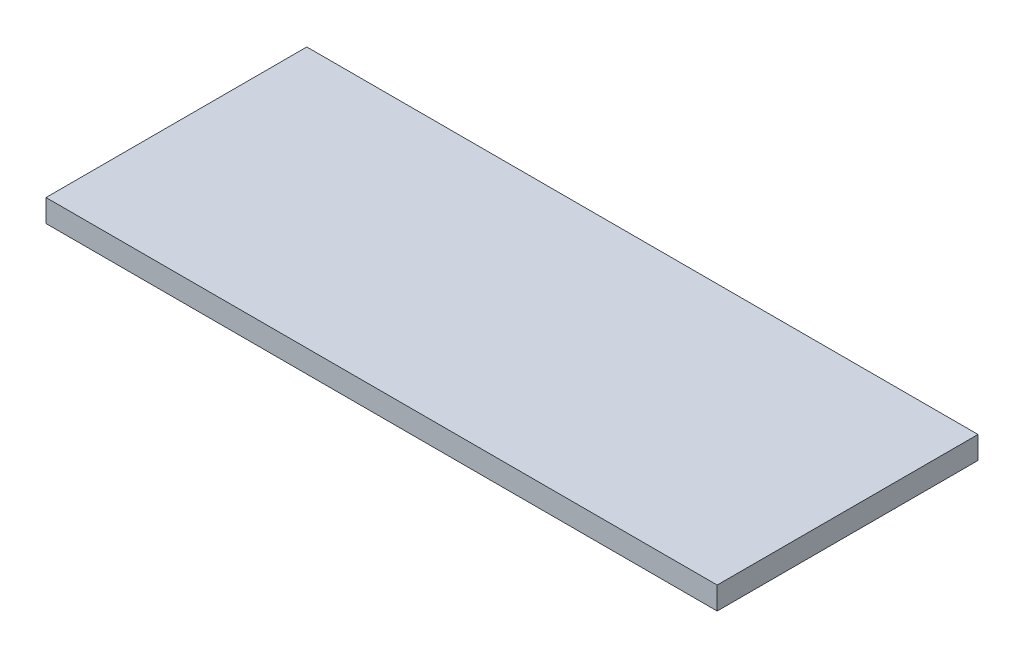
SolidWorks part; units mm, degrees
ref_plane "Front Plane" through (0, 0, 0) normal (0, 0, 1) x (1, 0, 0)
ref_plane "Top Plane" through (0, 0, 0) normal (0, 1, 0) x (1, 0, 0)
ref_plane "Right Plane" through (0, 0, 0) normal (1, 0, 0) x (0, 0, -1)
sketch "Sketch1" plane through (0, 0, 0) normal (0, 1, 0) x (1, 0, 0)
  line L1 (-44.65, 17.35) -> (44.65, 17.35)
  line L2 (-44.65, 17.35) -> (-44.65, -17.35)
  line L3 (-44.65, -17.35) -> (44.65, -17.35)
  line L4 (44.65, 17.35) -> (44.65, -17.35)
  line L5 (-44.65, 17.35) -> (44.65, -17.35) construction
  line L6 (-44.65, -17.35) -> (44.65, 17.35) construction
  point P0 (0, 0)
extrude "Boss-Extrude1" add sketch "Sketch1" along normal blind 3
